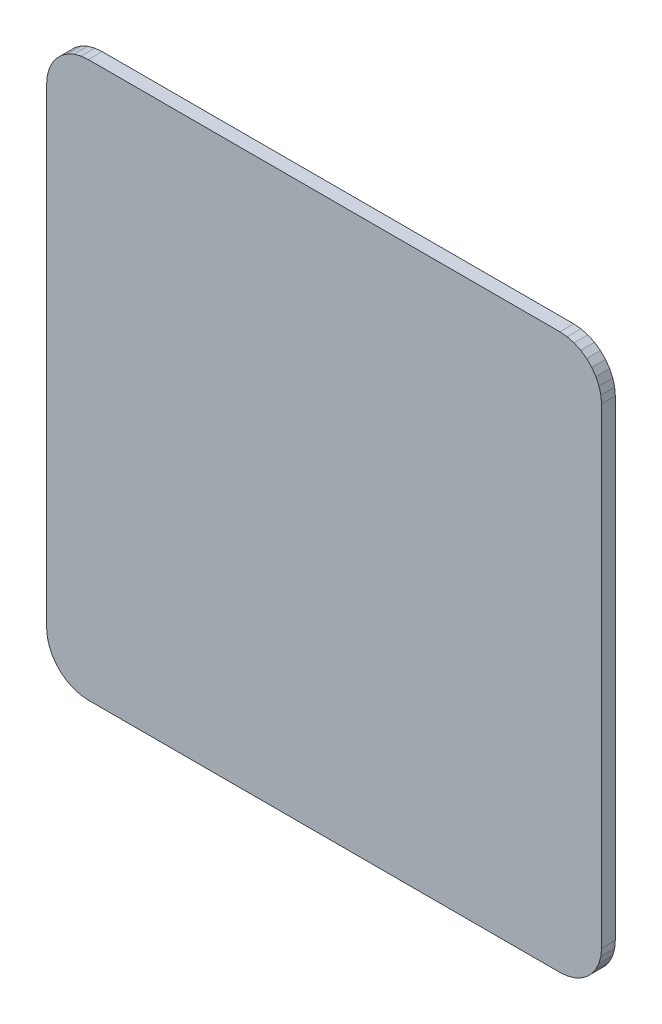
SolidWorks part; units mm, degrees
ref_plane "Front Plane" through (0, 0, 0) normal (0, 0, 1) x (1, 0, 0)
ref_plane "Top Plane" through (0, 0, 0) normal (0, 1, 0) x (1, 0, 0)
ref_plane "Right Plane" through (0, 0, 0) normal (1, 0, 0) x (0, 0, -1)
sketch "Sketch1" plane through (0, 0, 0) normal (0, 0, 1) x (1, 0, 0)
  line L0 (238.7374, 111.8768) -> (272.7374, 111.8768)
  line L1 (272.7374, 111.8768) -> (273.2583, 111.9224)
  line L2 (273.2583, 111.9224) -> (273.7635, 112.0577)
  line L3 (273.7635, 112.0577) -> (274.2374, 112.2787)
  line L4 (274.2374, 112.2787) -> (274.6658, 112.5787)
  line L5 (274.6658, 112.5787) -> (275.0355, 112.9484)
  line L6 (275.0355, 112.9484) -> (275.3355, 113.3768)
  line L7 (275.3355, 113.3768) -> (275.5565, 113.8508)
  line L8 (275.5565, 113.8508) -> (275.6918, 114.3559)
  line L9 (275.6918, 114.3559) -> (275.7374, 114.8768)
  line L10 (275.7374, 114.8768) -> (275.7374, 148.8768)
  line L11 (275.7374, 148.8768) -> (275.6918, 149.3977)
  line L12 (275.6918, 149.3977) -> (275.5565, 149.9029)
  line L13 (275.5565, 149.9029) -> (275.3355, 150.3768)
  line L14 (275.3355, 150.3768) -> (275.0355, 150.8052)
  line L15 (275.0355, 150.8052) -> (274.6658, 151.1749)
  line L16 (274.6658, 151.1749) -> (274.2374, 151.4749)
  line L17 (274.2374, 151.4749) -> (273.7635, 151.6959)
  line L18 (273.7635, 151.6959) -> (273.2583, 151.8312)
  line L19 (273.2583, 151.8312) -> (272.7374, 151.8768)
  line L20 (272.7374, 151.8768) -> (238.7374, 151.8768)
  line L21 (238.7374, 151.8768) -> (238.2165, 151.8312)
  line L22 (238.2165, 151.8312) -> (237.7114, 151.6959)
  line L23 (237.7114, 151.6959) -> (237.2374, 151.4749)
  line L24 (237.2374, 151.4749) -> (236.809, 151.1749)
  line L25 (236.809, 151.1749) -> (236.4393, 150.8052)
  line L26 (236.4393, 150.8052) -> (236.1393, 150.3768)
  line L27 (236.1393, 150.3768) -> (235.9183, 149.9029)
  line L28 (235.9183, 149.9029) -> (235.783, 149.3977)
  line L29 (235.783, 149.3977) -> (235.7374, 148.8768)
  line L30 (235.7374, 148.8768) -> (235.7374, 114.8768)
  line L31 (235.7374, 114.8768) -> (235.783, 114.3559)
  line L32 (235.783, 114.3559) -> (235.9183, 113.8508)
  line L33 (235.9183, 113.8508) -> (236.1393, 113.3768)
  line L34 (236.1393, 113.3768) -> (236.4393, 112.9484)
  line L35 (236.4393, 112.9484) -> (236.809, 112.5787)
  line L36 (236.809, 112.5787) -> (237.2374, 112.2787)
  line L37 (237.2374, 112.2787) -> (237.7114, 112.0577)
  line L38 (237.7114, 112.0577) -> (238.2165, 111.9224)
  line L39 (238.2165, 111.9224) -> (238.7374, 111.8768)
extrude "Board" add sketch "Sketch1" along normal blind 0.9954
sketch "Sketch2" plane through (0, 0, 0.9954) normal (0, 0, 1) x (1, 0, 0)
  line L0 (173.9138, 63.754) -> (414.0454, 63.754)
  line L1 (414.0454, 63.754) -> (414.0454, 83.7692)
  line L2 (414.0454, 83.7692) -> (173.9138, 83.7692)
  line L3 (173.9138, 83.7692) -> (173.9138, 63.754)
surface "TOP" sketch "Sketch2"
